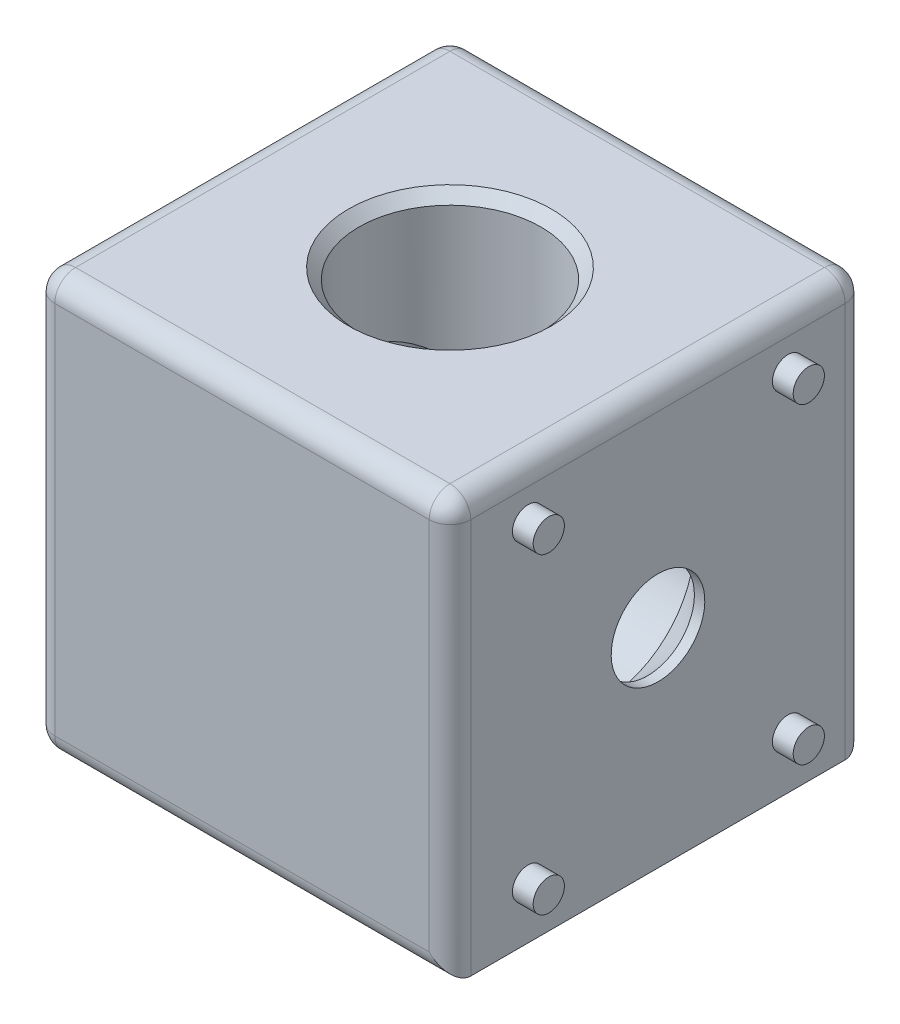
SolidWorks part; units mm, degrees
material "Алюминиевый сплав"
ref_plane "Спереди" through (0, 0, 0) normal (0, 0, 1) x (1, 0, 0)
ref_plane "Сверху" through (0, 0, 0) normal (0, 1, 0) x (1, 0, 0)
ref_plane "Справа" through (0, 0, 0) normal (1, 0, 0) x (0, 0, -1)
sketch "Эскиз1" plane through (0, 0, 0) normal (0, 1, 0) x (1, 0, 0)
  line L1 (-20, -20) -> (20, -20)
  line L2 (-20, -20) -> (-20, 20)
  line L3 (-20, 20) -> (20, 20)
  line L4 (20, -20) -> (20, 20)
  line L5 (-20, -20) -> (20, 20) construction
  line L6 (-20, 20) -> (20, -20) construction
  point P0 (0, 0)
  dimension "D1" = 40
extrude "Бобышка-Вытянуть1" add sketch "Эскиз1" along normal mid plane 40
sketch "Эскиз4" plane through (0, 0, 0) normal (0, 0, 1) x (1, 0, 0)
  line L0 (-4.5, -20) -> (-4.5, -19)
  line L1 (-20, -20) -> (20, -20) construction
  line L2 (-4.5, -19) -> (-8.75, -14.75)
  line L3 (-8.75, -14.75) -> (-8.75, 19)
  line L4 (-20, 20) -> (20, 20) construction
  line L6 (0, 20) -> (0, -20) construction
  line L7 (0, -20) -> (-4.5, -20)
  line L8 (0, 20) -> (0, -20)
  line L9 (-8.75, 19) -> (-9.75, 20)
  line L10 (-9.75, 20) -> (0, 20)
  dimension "D1" = 9
  dimension "D2" = 45
  dimension "D3" = 17.5
  dimension "D4" = 1
  dimension "D5" = 1
revolve "Вырез-Повернуть1" cut sketch "Эскиз4" angle 360 about L6
sketch "Эскиз5" plane through (0, -20, 0) normal (0, -1, 0) x (1, 0, 0)
  line L1 (-15, 12.5) -> (15, 12.5) construction
  line L2 (-15, 12.5) -> (-15, -12.5) construction
  line L3 (-15, -12.5) -> (15, -12.5) construction
  line L4 (15, 12.5) -> (15, -12.5) construction
  circle A0 centre (-15, 12.5) radius 1.5
  circle A1 centre (-15, -12.5) radius 1.5
  circle A2 centre (15, -12.5) radius 1.5
  circle A3 centre (15, 12.5) radius 1.5
  point P5 (-15, 0)
  point P12 (0, 12.5)
  dimension "D1" = 3
  dimension "D2" = 30
  dimension "D3" = 25
extrude "Бобышка-Вытянуть2" add sketch "Эскиз5" along normal blind 2
ref_plane "Плоскость1" through (0, 0, 0) normal (0.7071, 0.7071, 0) x (0.7071, -0.7071, 0)
mirror "Зеркальное отражение1" about plane through (0, 0, 0) normal (0.7071, 0.7071, 0) of "Бобышка-Вытянуть2", "Вырез-Повернуть1"
fillet "Скругление1" radius 2 11 edges at (-20, -20, 0) (20, 20, 0) (-20, 0, 20) (0, 20, 20) (-20, 20, 0) (-20, 0, -20) (0, 20, -20) (0, -20, -20) (20, 0, -20) (0, -20, 20) (20, 0, 20)
